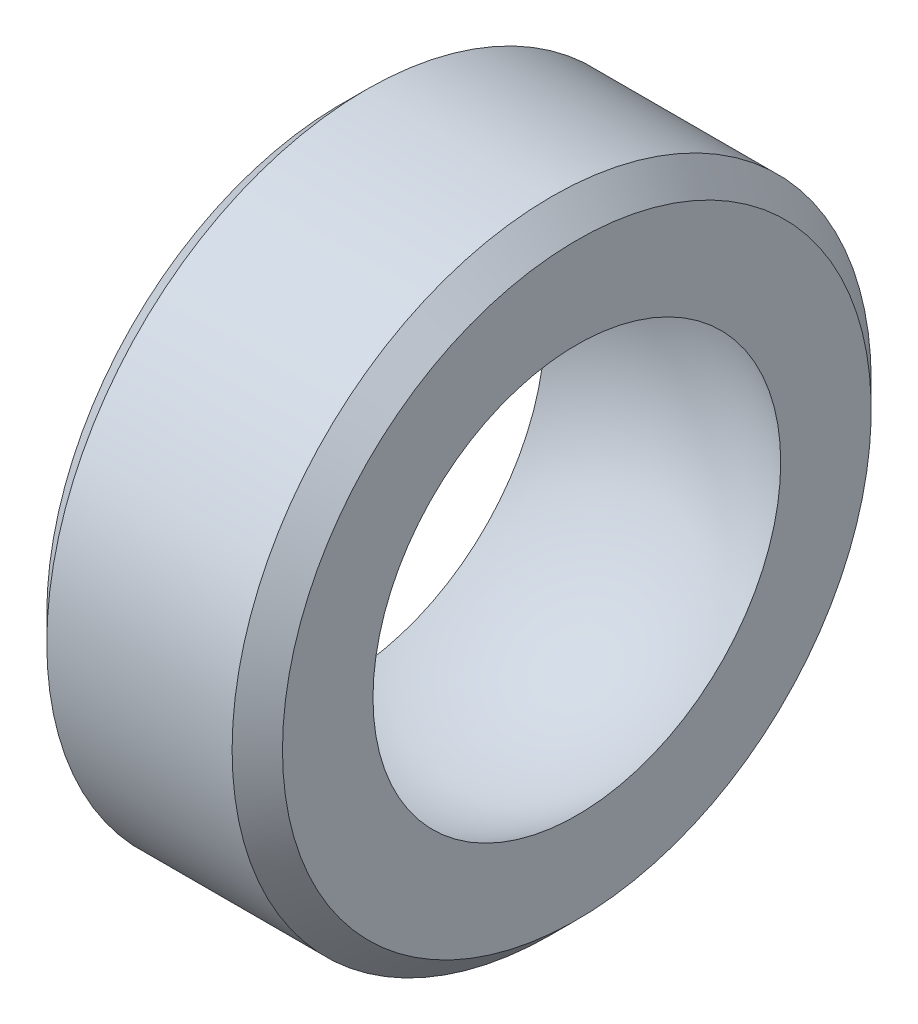
SolidWorks part; units mm, degrees
material "AISI 304"
ref_plane "Front Plane" through (0, 0, 0) normal (0, 0, 1) x (1, 0, 0)
ref_plane "Top Plane" through (0, 0, 0) normal (0, 1, 0) x (1, 0, 0)
ref_plane "Right Plane" through (0, 0, 0) normal (1, 0, 0) x (0, 0, -1)
sketch "Sketch1" plane through (0, 0, 0) normal (0, 0, 1) x (1, 0, 0)
  line L0 (-3.555, 0) -> (0, 0) construction
  line L1 (0, 0) -> (3.555, 0) construction
  line L2 (0, 0) -> (0, 7.1036) construction
  line L3 (-3.555, 6.15) -> (-3.555, 8.88)
  line L4 (-2.795, 9.64) -> (2.795, 9.64)
  line L5 (3.555, 8.88) -> (3.555, 6.15)
  line L6 (-3.555, 8.88) -> (-2.795, 9.64)
  line L7 (2.795, 9.64) -> (3.555, 8.88)
  arc A0 (-3.555, 6.15) -> (3.555, 6.15) centre (0, 0) cw
  point P5 (-3.555, 9.64)
  point P8 (3.555, 9.64)
  point P10 (0, 9.64)
  point P11 (0, 0)
  point P12 (0, 0.1938)
  point P16 (0, 9.64)
  point P17 (0, 7.1036)
  dimension "D4" = 7.1036
  dimension "D1" = 19.28
  dimension "D2" = 7.11
  dimension "D3" = 12.3
revolve "Revolve1" add sketch "Sketch1" angle 360 about L0
